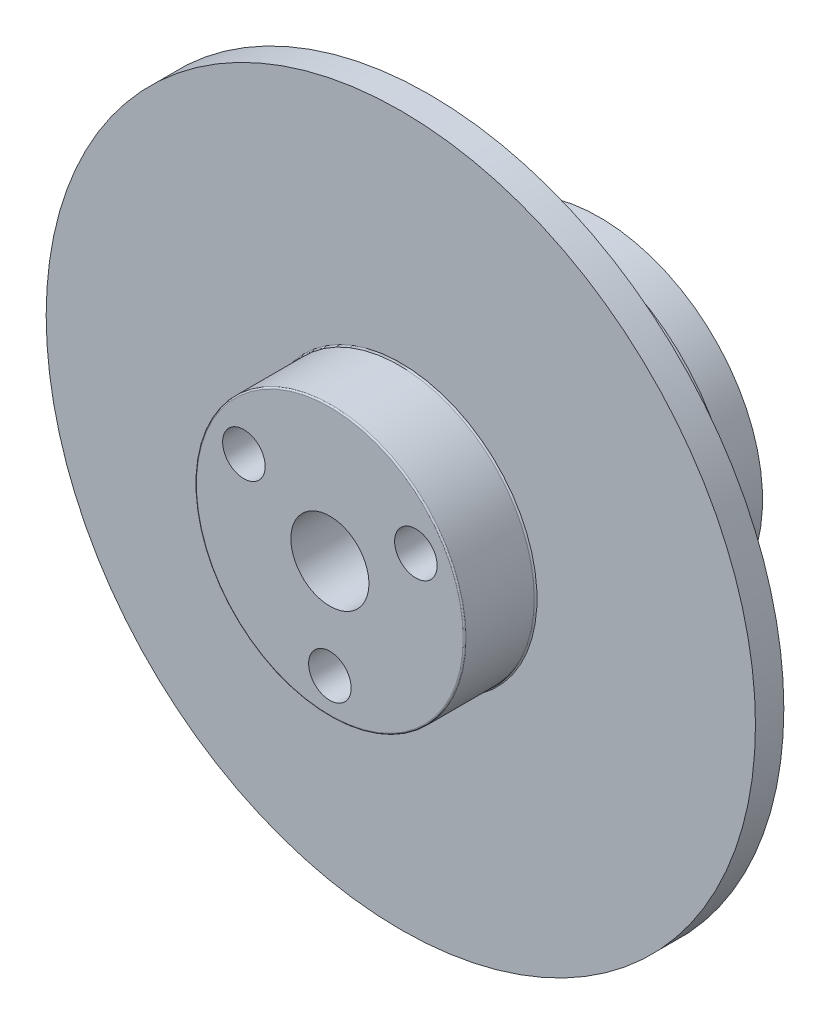
SolidWorks part; units mm, degrees
other "마크업1"
sketch "스케치14" plane through (30, 31, -30.5354) normal (0.2605, 0.9636, -0.0594) x (0.9655, -0.2601, 0.014)
sketch "스케치15" plane through (30, 31, -30.5354) normal (0.2605, 0.9636, -0.0594) x (0.9655, -0.2601, 0.014)
sketch "스케치16" plane through (30, 31, -30.5354) normal (0.2605, 0.9636, -0.0594) x (0.9655, -0.2601, 0.014)
sketch "스케치21" plane through (30, 31, -30.5354) normal (0.2605, 0.9636, -0.0594) x (0.9655, -0.2601, 0.014)
sketch "스케치23" plane through (30, 275, -27) normal (0.2605, 0.9636, -0.0594) x (0.9655, -0.2601, 0.014)
sketch "스케치28" plane through (20, 265, -24) normal (0.2605, 0.9636, -0.0594) x (0.9655, -0.2601, 0.014)
sketch "스케치31" plane through (20, 265, -24) normal (0.2605, 0.9636, -0.0594) x (0.9655, -0.2601, 0.014)
sketch "스케치32" plane through (20, 265, -23) normal (0.2605, 0.9636, -0.0594) x (0.9655, -0.2601, 0.014)
sketch "스케치33" plane through (20, 265, -23) normal (0.2605, 0.9636, -0.0594) x (0.9655, -0.2601, 0.014)
sketch "스케치38" plane through (25, 25, -31) normal (0.2605, 0.9636, -0.0594) x (0.9655, -0.2601, 0.014)
sketch "스케치39" plane through (25, 25, -31) normal (0.2605, 0.9636, -0.0594) x (0.9655, -0.2601, 0.014)
sketch "스케치40" plane through (25, 25, -31) normal (0.2605, 0.9636, -0.0594) x (0.9655, -0.2601, 0.014)
sketch "스케치47" plane through (25, 25, -31) normal (0.2605, 0.9636, -0.0594) x (0.9655, -0.2601, 0.014)
sketch "스케치54" plane through (25, 25, -14) normal (0.2605, 0.9636, -0.0594) x (0.9655, -0.2601, 0.014)
sketch "스케치55" plane through (25, 25, -14) normal (0.2605, 0.9636, -0.0594) x (0.9655, -0.2601, 0.014)
sketch "스케치56" plane through (25, 25, -15) normal (0.2605, 0.9636, -0.0594) x (0.9655, -0.2601, 0.014)
sketch "스케치57" plane through (25, 25, -14) normal (0.2605, 0.9636, -0.0594) x (0.9655, -0.2601, 0.014)
sketch "스케치58" plane through (25, 25, -14) normal (0.2605, 0.9636, -0.0594) x (0.9655, -0.2601, 0.014)
sketch "스케치59" plane through (25, 25, -11) normal (0.2605, 0.9636, -0.0594) x (0.9655, -0.2601, 0.014)
sketch "스케치60" plane through (25, 25, -14) normal (0.2605, 0.9636, -0.0594) x (0.9655, -0.2601, 0.014)
sketch "스케치63" plane through (25, 25, -14) normal (0.2605, 0.9636, -0.0594) x (0.9655, -0.2601, 0.014)
sketch "스케치64" plane through (25, 25, -14) normal (0.2605, 0.9636, -0.0594) x (0.9655, -0.2601, 0.014)
sketch "스케치68" plane through (25, 25, -14) normal (0.2605, 0.9636, -0.0594) x (0.9655, -0.2601, 0.014)
sketch "스케치80" plane through (25, 25, -14) normal (0.2605, 0.9636, -0.0594) x (0.9655, -0.2601, 0.014)
sketch "스케치81" plane through (25, 25, -14) normal (0.2605, 0.9636, -0.0594) x (0.9655, -0.2601, 0.014)
sketch "스케치90" plane through (25, 25, -14) normal (0.2605, 0.9636, -0.0594) x (0.9655, -0.2601, 0.014)
material "7075-T6 (SN)"
ref_plane "정면" through (0, 0, 0) normal (0, 0, 1) x (1, 0, 0)
ref_plane "윗면" through (0, 0, 0) normal (0, 1, 0) x (1, 0, 0)
ref_plane "우측면" through (0, 0, 0) normal (1, 0, 0) x (0, 0, -1)
sketch "스케치2" plane through (0, 6, 0) normal (0, 0, -1) x (1, 0, 0)
  circle A0 centre (0, 6) radius 10
  circle A1 centre (0, 6) radius 25
  dimension "D1" = 50
  dimension "30" = 20
extrude "보스-돌출2" add sketch "스케치2" along normal blind 2
sketch "스케치35" plane through (0, 0, -2) normal (0, 0, -1) x (-1, 0, 0)
  circle A0 centre (0, 0) radius 13.5
  dimension "D1" = 27
extrude "보스-돌출3" add sketch "스케치35" along normal blind 2
sketch "스케치36" plane through (0, 0, -4) normal (0, 0, -1) x (-1, 0, 0)
  circle A0 centre (0, 0) radius 12.5
  dimension "D1" = 25
extrude "보스-돌출4" add sketch "스케치36" along normal blind 7
sketch "스케치46" plane through (0, 0, -11) normal (0, 0, -1) x (-1, 0, 0)
  circle A0 centre (0, 0) radius 4 construction
  circle A1 centre (0, 4) radius 2.25
  dimension "D1" = 8
  dimension "D2" = 4.5
hole_wizard "M3 육각 소켓 머리 캡 나사용 카운터보어1" positions "스케치48" profile "스케치49" counterbore size "M3" standard "ISO" end condition through all
sketch "스케치48" plane through (0, 0, -11) normal (0, 0, -1) x (-1, 0, 0)
  point P0 (0, 4)
sketch "스케치49" plane through (0, 4, -11) normal (1, 0, 0) x (0, 1, 0)
  line L0 (0, 0) -> (0, 11)
  line L1 (0, 11) -> (1.7, 11)
  line L3 (1.7, 11) -> (1.7, 3.4)
  line L4 (1.7, 3.4) -> (3.25, 3.4)
  line L5 (3.25, 3.4) -> (3.25, 0)
  line L7 (3.25, 0) -> (0, 0)
  line L11 (0, -6.35) -> (0, 107.95) construction
  dimension "관통 구멍 지름" = 3.4
  dimension "관통 구멍 깊이" = 11
  dimension "카운터보어 지름" = 6.5
  dimension "카운터보어 깊이" = 3.4
pattern_circular "원형 패턴1" count 3 over 360 about axis through (0, 0, 0) along (0, 0, 1) of "M3 육각 소켓 머리 캡 나사용 카운터보어1"
sketch "스케치50" plane through (0, 0, -11) normal (0, 0, -1) x (-1, 0, 0)
  circle A1 centre (0, 0) radius 7
  point P3 (0, -7)
  dimension "D1" = 14
hole_wizard "M3 탭을 위한 탭 드릴1" positions "스케치51" profile "스케치52" hole size "M3" standard "ISO"
sketch "스케치51" plane through (0, 0, -11) normal (0, 0, -1) x (-1, 0, 0)
  point P0 (0, -7)
sketch "스케치52" plane through (0, -7, -11) normal (1, 0, 0) x (0, 1, 0)
  line L0 (0, 0) -> (0, 5.7511)
  line L1 (0, 5.7511) -> (1.25, 5)
  line L2 (1.25, 5) -> (1.25, 0)
  line L5 (1.25, 0) -> (0, 0)
  line L10 (0, 5.7511) -> (-1.25, 5) construction
  line L11 (0, -6.35) -> (0, 107.95) construction
  dimension "구멍 지름" = 2.5
  dimension "구멍 깊이" = 5
  dimension "드릴 각도" = 118
pattern_circular "원형 패턴2" count 3 over 360 about axis through (0, 0, 0) along (0, 0, 1) of "M3 탭을 위한 탭 드릴1"
sketch "스케치53" plane through (0, 0, -11) normal (0, 0, -1) x (-1, 0, 0)
  circle A0 centre (0, 0) radius 11.5
  circle A1 centre (0, -7) radius 1.25 construction
  circle A2 centre (0, 0) radius 12.5
  circle A3 centre (0, 0) radius 12.5
  circle A4 centre (-3.4641, -2) radius 3.25 construction
  circle A5 centre (-6.0622, 3.5) radius 1.25 construction
  circle A6 centre (6.0622, 3.5) radius 1.25 construction
  circle A7 centre (3.4641, -2) radius 3.25 construction
  circle A8 centre (0, 4) radius 3.25 construction
  circle A9 centre (0, -7) radius 1.25
  circle A10 centre (-3.4641, -2) radius 3.25
  circle A11 centre (-6.0622, 3.5) radius 1.25
  circle A12 centre (6.0622, 3.5) radius 1.25
  circle A13 centre (3.4641, -2) radius 3.25
  circle A14 centre (0, 4) radius 3.25
  circle M2 centre (6.0622, 3.5) radius 1.25
  circle M3 centre (-6.0622, 3.5) radius 1.25
  circle M4 centre (0, -7) radius 1.25
  circle M5 centre (-3.4641, -2) radius 3.25
  circle M6 centre (3.4641, -2) radius 3.25
  circle M7 centre (0, 4) radius 3.25
  dimension "D1" = 23
  dimension "D2" = 0
extrude "보스-돌출5" add sketch "스케치53" along normal blind 3 contours A0 M2 M4 M6 M7 M5 M3
sketch "스케치61" plane through (0, 0, -2) normal (0, 0, 1) x (1, 0, 0)
  circle A0 centre (0, 0) radius 10
  circle A1 centre (0, 0) radius 10 construction
  circle A2 centre (-3.4641, -2) radius 1.7
  circle A3 centre (3.4641, -2) radius 1.7
  circle A4 centre (0, 4) radius 1.7
  circle A5 centre (0, 4) radius 1.7 construction
  circle A6 centre (-3.4641, -2) radius 1.7 construction
  circle A7 centre (3.4641, -2) radius 1.7 construction
extrude "보스-돌출6" add sketch "스케치61" along normal blind 7
sketch "스케치62" plane through (0, 0, 5) normal (0, 0, 1) x (1, 0, 0)
  circle A0 centre (0, 0) radius 9.5
  circle A1 centre (0, 0) radius 10
  circle A2 centre (0, 0) radius 10 construction
  dimension "D1" = 19
extrude "컷-돌출1" cut sketch "스케치62" against normal blind 5
fillet "필렛1" radius 0.1 2 edges at (9.5, 0, 0) (9.5, 0, 5)
sketch "스케치65" plane through (0, 0, 5) normal (0, 0, 1) x (1, 0, 0)
  circle A0 centre (0, 0) radius 7 construction
  dimension "D1" = 14
hole_wizard "Ø3.0mm 맞춤핀 구멍1" positions "스케치66" profile "스케치67" hole size "Ø3.0" standard "ISO"
sketch "스케치66" plane through (0, 0, 5) normal (0, 0, 1) x (1, 0, 0)
  circle A0 centre (0, 0) radius 7 construction
  point P0 (0, -7)
sketch "스케치67" plane through (0, -7, 5) normal (1, 0, 0) x (0, -1, 0)
  line L0 (0, 0) -> (0, 5.9013)
  line L1 (0, 5.9013) -> (1.5, 5)
  line L2 (1.5, 5) -> (1.5, 0)
  line L5 (1.5, 0) -> (0, 0)
  line L10 (0, 5.9013) -> (-1.5, 5) construction
  line L11 (0, -6.35) -> (0, 107.95) construction
  dimension "구멍 지름" = 3
  dimension "구멍 깊이" = 5
  dimension "드릴 각도" = 118
pattern_circular "원형 패턴3" count 3 over 360 about axis through (0, 0, 0) along (0, 0, 1) of "Ø3.0mm 맞춤핀 구멍1"
sketch "스케치69" plane through (0, 0, 5) normal (0, 0, 1) x (1, 0, 0)
  circle A0 centre (0, 0) radius 3.5 construction
  dimension "D1" = 7
sketch "스케치73" plane through (0, 0, -14) normal (0, 0, -1) x (-1, 0, 0)
  line L0 (0, 0) -> (0, 30.1914) construction
  line L1 (-30.644, 0) -> (39.9407, 0) construction
  circle A0 centre (0, 0) radius 8.5 construction
  point P6 (0, 8.5)
  dimension "D2" = 17
  dimension "D1" = 90
sketch "스케치82" plane through (0, 0, -14) normal (0, 0, -1) x (-1, 0, 0)
  circle A0 centre (0, 4) radius 3.25
  circle A1 centre (0, 4) radius 3.25 construction
  circle A2 centre (-3.4641, -2) radius 3.25
  circle A3 centre (-3.4641, -2) radius 3.25 construction
  circle A4 centre (3.4641, -2) radius 3.25
  circle A5 centre (3.4641, -2) radius 3.25 construction
extrude "보스-돌출7" add sketch "스케치82" against normal blind 19
hole_wizard "M5 육각 소켓 머리 캡 나사용 카운터보어1" positions "스케치83" profile "스케치85" counterbore size "M5" standard "ISO" end condition through all
sketch "스케치83" plane through (0, 0, -14) normal (0, 0, -1) x (-1, 0, 0)
  point P0 (0, 0)
sketch "스케치85" plane through (0, 0, -14) normal (1, 0, 0) x (0, 1, 0)
  line L0 (0, 0) -> (0, 19)
  line L1 (0, 19) -> (2.75, 19)
  line L3 (2.75, 19) -> (2.75, 5.4)
  line L4 (2.75, 5.4) -> (5, 5.4)
  line L5 (5, 5.4) -> (5, 0)
  line L7 (5, 0) -> (0, 0)
  line L11 (0, -6.35) -> (0, 107.95) construction
  dimension "관통 구멍 지름" = 5.5
  dimension "관통 구멍 깊이" = 19
  dimension "카운터보어 지름" = 10
  dimension "카운터보어 깊이" = 5.4
hole_wizard "Ø3.0mm 맞춤핀 구멍2" positions "스케치88" profile "스케치89" hole size "Ø3.0" standard "ISO"
sketch "스케치88" plane through (0, 0, -14) normal (0, 0, -1) x (-1, 0, 0)
  point P0 (0, 8.5)
sketch "스케치89" plane through (0, 8.5, -14) normal (1, 0, 0) x (0, 1, 0)
  line L0 (0, 0) -> (0, 5.9013)
  line L1 (0, 5.9013) -> (1.5, 5)
  line L2 (1.5, 5) -> (1.5, 0)
  line L5 (1.5, 0) -> (0, 0)
  line L10 (0, 5.9013) -> (-1.5, 5) construction
  line L11 (0, -6.35) -> (0, 107.95) construction
  dimension "구멍 지름" = 3
  dimension "구멍 깊이" = 5
  dimension "드릴 각도" = 118
pattern_circular "원형 패턴4" count 3 over 360 about axis through (0, 0, 0) along (0, 0, 1) of "Ø3.0mm 맞춤핀 구멍2"
